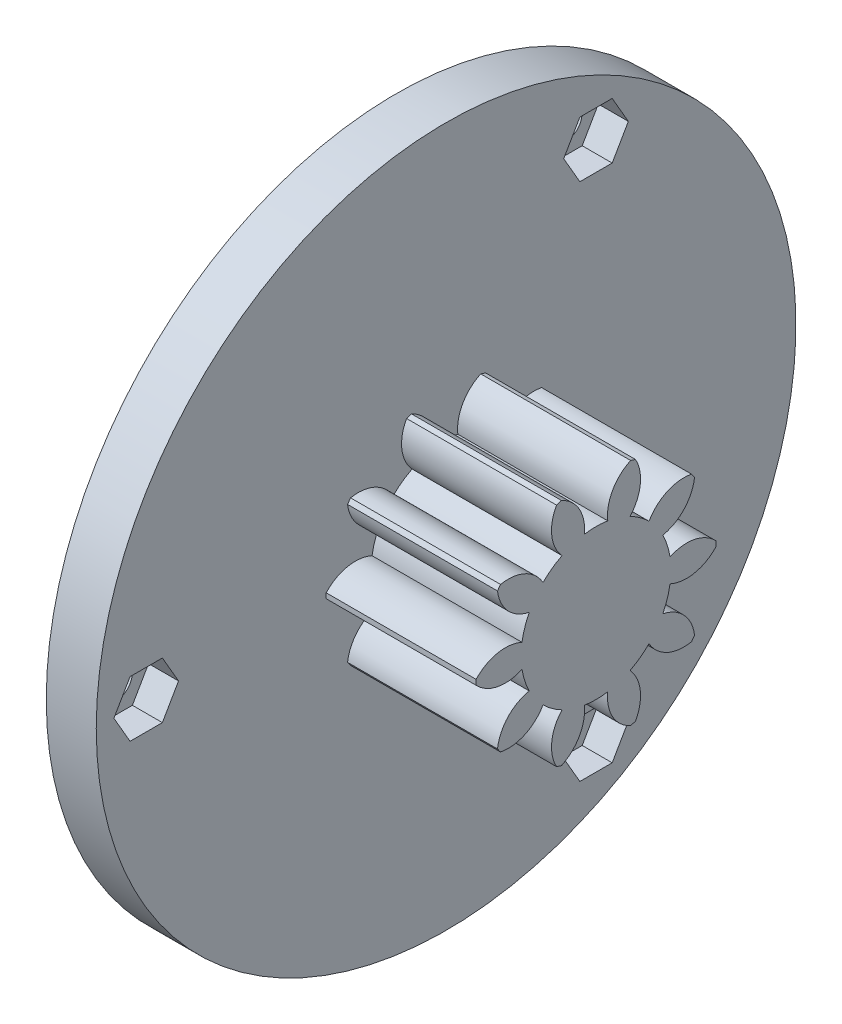
SolidWorks part; units mm, degrees
ref_plane "Plane1" through (0, 0, 0) normal (0, 0, 1) x (1, 0, 0)
ref_plane "Plane2" through (0, 0, 0) normal (0, 1, 0) x (1, 0, 0)
ref_plane "Plane3" through (0, 0, 0) normal (1, 0, 0) x (0, 0, -1)
other "Configuration Table"
sketch "HoldingSke" plane through (0, 0, 0) normal (0, 1, 0) x (1, 0, 0)
  line L0 (0, 0) -> (0.4924, -0.0868)
  line L1 (-15, 0) -> (100, 0) construction
  line L2 (0, 0) -> (-2.1039, 2.3779)
  line L3 (0, 0) -> (-11.863, 4.5341)
  line L4 (0, 0) -> (8.5048, 1.4996)
  line L5 (0, 0) -> (-46.8476, -17.4728)
  line L6 (0, 0) -> (-12.4344, -8.3896)
  line L7 (-2.1039, 2.3779) -> (8.6586, 51.2059)
  line L8 (-76.2, 54.61) -> (-76.1, 54.61)
  line L9 (-71.009, 38.7566) -> (-53.1078, 45.2721)
  line L10 (-76.2, 71.12) -> (104.1128, 71.12)
  line L11 (0, 0) -> (-15, 0)
  line L12 (-76.2, 101.6) -> (-76.133, 101.6)
  line L13 (24.9733, 27.94) -> (52.9518, 28.4284)
  line L14 (24.9733, 27.94) -> (24.9743, 27.94)
  line L15 (24.9733, 27.94) -> (100.4006, 29.5858)
  line L16 (-63.627, -2) -> (-12.827, -2)
  circle A0 centre (0, 0) radius 0.45
  circle A1 centre (0, 0) radius 7.499
  circle A2 centre (0, 0) radius 37.5
  circle A3 centre (0, 0) radius 0.45
  dimension "MHD" = 14.998
  dimension "Hub_dia" = 75
  dimension "Bore" = 0.9
  dimension "MBD" = 0.9
  dimension "Num_teeth" = 10
  dimension "Pitch" = 0.5
  dimension "Overall_len" = 50
  dimension "Show_teeth" = 10
  dimension "Thickness" = 15
  dimension "OAL" = 50.0001
  dimension "T_dim" = 0.1
  dimension "Ap" = 20
  dimension "H" = 19.05
  dimension "Pitch_radius" = 180.3128
  dimension "Width" = 15
  dimension "Backlash" = 0.067
  dimension "Addendum_fac" = 1
  dimension "Dedendum_fac" = 1.25
  dimension "Clearance_fac" = 0.25
  dimension "Dedendum_add" = 0.001
  dimension "Module" = 2
sketch "BasProSke" plane through (0, 0, 0) normal (0, 1, 0) x (1, 0, 0)
  line L0 (-10, 0) -> (60, 0) construction
  line L1 (0, 0) -> (0, 12)
  line L2 (0, 0) -> (15, 0)
  line L3 (15, 0) -> (15, 12)
  line L4 (15, 12) -> (0, 12)
  dimension "Thickness" = 15
  dimension "Diameter" = 24
revolve "Base-Revolve" add sketch "BasProSke" angle 360 about L0
sketch "TooCutSke" plane through (0, 0, 0) normal (1, 0, 0) x (0, 0, -1)
  line L1 (0, 0) -> (0, 107) construction
  line L2 (0, 0) -> (-1.6814, 9.8576) construction
  line L3 (0, 0) -> (-6.1153, 18.8209) construction
  line L4 (-1.6814, 9.8576) -> (-3.0576, 9.4105) construction
  arc A0 (1.1737, 7.4066) -> (-1.1737, 7.4066) centre (0, 0) ccw
  arc A1 (3.4979, 11.5054) -> (-3.4979, 11.5054) centre (0, 0) ccw
  circle A2 centre (0, 0) radius 10 construction
  circle A3 centre (0, 0) radius 9.3969 construction
  arc A4 (-1.1737, 7.4066) -> (-3.4979, 11.5054) centre (-5.1477, 7.8615) ccw
  arc A5 (3.4979, 11.5054) -> (1.1737, 7.4066) centre (5.1477, 7.8615) ccw
  dimension "Root_dia" = 14.998
  dimension "Overcut_dia" = 24.0508
  dimension "Pitch_dia" = 20
  dimension "Base_dia" = 18.7939
  dimension "Flank_rad" = 4
  dimension "Half_ang" = 18
  dimension "Half_CT" = 1.4471
extrude "ToothCut" cut sketch "TooCutSke" along normal through all
fillet "Breaks" [suppressed] radius 0.04
fillet "RootFillets" [suppressed] radius 0.501
pattern_circular "TeethCuts" count 10 every 36 about axis through (-10, 0, 0) along (1, 0, 0) of "ToothCut", "RootFillets", "Breaks"
sketch "HubNeaOneSke" plane through (0, 0, 0) normal (-1, 0, 0) x (0, 0, 1)
  circle A0 centre (0, 0) radius 7.499
  dimension "Diameter" = 14.998
extrude "HubNearOne" [suppressed] add sketch "HubNeaOneSke" along normal blind 35.0001
sketch "HubNeaBotSke" plane through (0, 0, 0) normal (-1, 0, 0) x (0, 0, 1)
  circle A0 centre (0, 0) radius 7.499
  dimension "Diameter" = 14.998
extrude "HubNearBoth" [suppressed] add sketch "HubNeaBotSke" along normal blind 17.5
ref_plane "FarPln" through (15, 0, 0) normal (1, 0, 0) x (0, 0, -1)
sketch "HubFarSke" plane through (15, 0, 0) normal (1, 0, 0) x (0, 0, -1)
  circle A0 centre (0, 0) radius 7.499
  dimension "Diameter" = 14.998
extrude "HubFar" [suppressed] add sketch "HubFarSke" along normal blind 17.5
sketch "BorSke" plane through (0, 0, 0) normal (1, 0, 0) x (0, 0, -1)
  circle A0 centre (0, 0) radius 0.45
  dimension "Diameter" = 0.9
extrude "Bore" cut sketch "BorSke" along normal mid plane 100.0001
sketch "KeySke" plane through (0, 0, 0) normal (1, 0, 0) x (0, 0, -1)
  line L0 (-0.05, 0) -> (-0.05, 0.55)
  line L1 (-0.05, 0.55) -> (0.05, 0.55)
  line L2 (0.05, 0.55) -> (0.05, 0)
  line L3 (0, 0) -> (0, 34) construction
  line L4 (-0.05, 0) -> (0.05, 0)
  dimension "Offset" = 0.55
  dimension "Width" = 0.1
extrude "Keyway" [suppressed] cut sketch "KeySke" along normal mid plane 100.0001
pattern_circular "Keyway2" [suppressed] count 2 every 90 about axis through (-10, 0, 0) along (1, 0, 0)
sketch "Sketch1" plane through (0, 0, 0) normal (-1, 0, 0) x (0, 0, 1)
  line L0 (0, 0) -> (0, 2.3) construction
  line L1 (-1.2124, 2.3) -> (1.2124, 2.3)
  circle A0 centre (0, 0) radius 2.6
  point P7 (0, 2.3)
extrude "Cut-Extrude1" cut sketch "Sketch1" against normal blind 15
sketch "Sketch2" plane through (0, 0, 0) normal (-1, 0, 0) x (0, 0, 1)
  circle A0 centre (0, 0) radius 3.9911
extrude "Boss-Extrude1" add sketch "Sketch2" against normal blind 15
sketch "Sketch3" plane through (0, 0, 0) normal (-1, 0, 0) x (0, 0, 1)
  circle A0 centre (0, 0) radius 35
extrude "Boss-Extrude2" add sketch "Sketch3" along normal blind 5
sketch "Sketch7" plane through (-5, 0, 0) normal (-1, 0, 0) x (0, 0, 1)
  circle A0 centre (0, 0) radius 30
  circle A2 centre (30, 0) radius 1.6
  circle A5 centre (-15, -25.9808) radius 1.6
  circle A6 centre (-15, 25.9808) radius 1.6
  point P12 (0, 0)
  point P14 (0, 0)
  dimension "D1" = 3
extrude "Cut-Extrude2" cut sketch "Sketch7" against normal blind 10 contours A6 | A2 | A5
sketch "Sketch8" plane through (0, 0, 0) normal (1, 0, 0) x (0, 0, -1)
  line L0 (15.8083, 27.3808) -> (14.1917, 27.3808)
  line L1 (-31.6166, 0) -> (-30.8083, -1.4)
  line L2 (-30.8083, -1.4) -> (-29.1917, -1.4)
  line L3 (-29.1917, -1.4) -> (-28.3834, 0)
  line L4 (-28.3834, 0) -> (-29.1917, 1.4)
  line L5 (-29.1917, 1.4) -> (-30.8083, 1.4)
  line L6 (-30.8083, 1.4) -> (-31.6166, 0)
  line L7 (14.1917, 27.3808) -> (13.3834, 25.9808)
  line L8 (13.3834, 25.9808) -> (14.1917, 24.5808)
  line L9 (14.1917, 24.5808) -> (15.8083, 24.5808)
  line L10 (15.8083, 24.5808) -> (16.6166, 25.9808)
  line L11 (16.6166, 25.9808) -> (15.8083, 27.3808)
  line L12 (15.8083, -27.3808) -> (16.6166, -25.9808)
  line L13 (16.6166, -25.9808) -> (15.8083, -24.5808)
  line L14 (15.8083, -24.5808) -> (14.1917, -24.5808)
  line L15 (14.1917, -24.5808) -> (13.3834, -25.9808)
  line L16 (13.3834, -25.9808) -> (14.1917, -27.3808)
  line L17 (14.1917, -27.3808) -> (15.8083, -27.3808)
  circle A0 centre (-30, 0) radius 1.4 construction
  point P24 (0, 0)
  dimension "D1" = 3
extrude "Cut-Extrude3" cut sketch "Sketch8" against normal blind 3
sketch "Sketch9" plane through (0, 0, 0) normal (1, 0, 0) x (0, 0, -1)
  line L0 (16.6166, 28.7808) -> (13.3834, 28.7808)
  line L1 (-33.2332, 0) -> (-31.6166, -2.8)
  line L2 (-31.6166, -2.8) -> (-28.3834, -2.8)
  line L3 (-28.3834, -2.8) -> (-26.7668, 0)
  line L4 (-26.7668, 0) -> (-28.3834, 2.8)
  line L5 (-28.3834, 2.8) -> (-31.6166, 2.8)
  line L6 (-31.6166, 2.8) -> (-33.2332, 0)
  line L7 (13.3834, 28.7808) -> (11.7668, 25.9808)
  line L8 (11.7668, 25.9808) -> (13.3834, 23.1808)
  line L9 (13.3834, 23.1808) -> (16.6166, 23.1808)
  line L10 (16.6166, 23.1808) -> (18.2332, 25.9808)
  line L11 (18.2332, 25.9808) -> (16.6166, 28.7808)
  line L12 (16.6166, -28.7808) -> (18.2332, -25.9808)
  line L13 (18.2332, -25.9808) -> (16.6166, -23.1808)
  line L14 (16.6166, -23.1808) -> (13.3834, -23.1808)
  line L15 (13.3834, -23.1808) -> (11.7668, -25.9808)
  line L16 (11.7668, -25.9808) -> (13.3834, -28.7808)
  line L17 (13.3834, -28.7808) -> (16.6166, -28.7808)
  circle A0 centre (-30, 0) radius 2.8 construction
  point P24 (0, 0)
  dimension "D1" = 3
extrude "Cut-Extrude5" cut sketch "Sketch9" against normal blind 3
equation "' \"Module@HoldingSke\" = 6.35"
equation "' \"Num_teeth@HoldingSke\" = 12"
equation "' \"Ap@HoldingSke\" =  20"
equation "' \"Ap@HoldingSke\" = 20"
equation "' \"Width@HoldingSke\" = 0.5 * 25.4"
equation "' \"Hub_dia@HoldingSke\"= 1 * 25.4"
equation "' \"Hub_dia@HoldingSke\" = 1 * 25.4"
equation "' \"Overall_len@HoldingSke\" = 1.0 * 25.4"
equation "' \"Bore@HoldingSke\" = 0.75 * 25.4"
equation "' \"T_dim@HoldingSke\" = 0.1 * 25.4"
equation "' \"Width@KeySke\" = 0.25 * 25.4"
equation "' \"Show_teeth@HoldingSke\" = 13"
equation "' \"Backlash@HoldingSke\" = 0.009 * 25.4"
equation "' \"Addendum_fac@HoldingSke\" = 1.0"
equation "' \"Dedendum_fac@HoldingSke\" = 1.25"
equation "' \"Dedendum_add@HoldingSke\" = 0.00005 * 25.4"
equation "' \"Clearance_fac@HoldingSke\" = 0.25"
equation "\"Pitch@HoldingSke\" = 1 / \"Module@HoldingSke\""
equation "\"Overcut_dia@TooCutSke\" = (\"Num_teeth@HoldingSke\" + 2 * \"Addendum_fac@HoldingSke\") / \"Pitch@HoldingSke\" + 0.002 * 25.4"
equation "\"Pitch_dia@TooCutSke\" = \"Num_teeth@HoldingSke\" / \"Pitch@HoldingSke\""
equation "\"Base_dia@TooCutSke\" = \"Num_teeth@HoldingSke\" / \"Pitch@HoldingSke\" * cos((\"Ap@HoldingSke\"  * 3.14159265 / 180))"
equation "\"Root_dia@TooCutSke\" = (\"Num_teeth@HoldingSke\" + 2) / \"Pitch@HoldingSke\" - 2 * (\"Addendum_fac@HoldingSke\" + \"Dedendum_fac@HoldingSke\") / \"Pitch@HoldingSke\" - \"Dedendum_add@HoldingSke\" * 2"
equation "\"Half_ang@TooCutSke\" = 180 / \"Num_teeth@HoldingSke\""
equation "\"Half_CT@TooCutSke\" = \"Num_teeth@HoldingSke\" / \"Pitch@HoldingSke\" * sin((3.14159265 / 2 / \"Num_teeth@HoldingSke\")) / 2 - 7 * \"Backlash@HoldingSke\" / 4"
equation "\"Flank_rad@TooCutSke\" = \"Num_teeth@HoldingSke\" / \"Pitch@HoldingSke\" / 5"
equation "\"Radius@RootFillets\" = \"Clearance_fac@HoldingSke\" / \"Pitch@HoldingSke\" + \"Dedendum_add@HoldingSke\""
equation "\"Break_rad@Breaks\" = 0.02 / \"Pitch@HoldingSke\""
equation "\"Thickness@HoldingSke\" = \"Width@HoldingSke\""
equation "\"OAL@HoldingSke\" = \"Thickness@HoldingSke\""
equation "\"MHD@HoldingSke\" = (\"Num_teeth@HoldingSke\" + 2) / \"Pitch@HoldingSke\" - 2 * (\"Addendum_fac@HoldingSke\" + \"Dedendum_fac@HoldingSke\")  / \"Pitch@HoldingSke\" - \"Dedendum_add@HoldingSke\" * 2"
equation "\"MBD@HoldingSke\" = (\"Num_teeth@HoldingSke\" + 2) / \"Pitch@HoldingSke\" - 2 * (\"Addendum_fac@HoldingSke\" + \"Dedendum_fac@HoldingSke\")  / \"Pitch@HoldingSke\" - \"Dedendum_add@HoldingSke\" * 2 - 0.002 * 25.4"
equation "\"MHD@HoldingSke\" = ((sgn( \"MHD@HoldingSke\" - \"Hub_dia@HoldingSke\" )-1)*( \"MHD@HoldingSke\" - \"Hub_dia@HoldingSke\" ))/-2+ \"Hub_dia@HoldingSke\""
equation "\"MBD@HoldingSke\" = ((sgn( \"MBD@HoldingSke\" - \"Bore@HoldingSke\" )-1)*( \"MBD@HoldingSke\" - \"Bore@HoldingSke\" ))/-2+ \"Bore@HoldingSke\""
equation "\"OAL@HoldingSke\" = ((sgn( \"OAL@HoldingSke\" - \"Overall_len@HoldingSke\" )+1)*( \"OAL@HoldingSke\" - \"Overall_len@HoldingSke\" ))/2 + \"Overall_len@HoldingSke\" + 0.000002 * 25.4"
equation "\"Num_teeth@TeethCuts\" = int( \"Show_teeth@HoldingSke\" ) + 1"
equation "\"Num_teeth@TeethCuts\" = ((sgn( \"Num_teeth@TeethCuts\" - \"Num_teeth@HoldingSke\" )-1)*( \"Num_teeth@TeethCuts\" - \"Num_teeth@HoldingSke\" ))/-2+ \"Num_teeth@HoldingSke\""
equation "\"Num_teeth@TeethCuts\" = ((sgn( \"Num_teeth@TeethCuts\" - 2.0)+1)*( \"Num_teeth@TeethCuts\" - 2.0))/2 +2.0"
equation "\"Angle@TeethCuts\" = 360.0 / \"Num_teeth@HoldingSke\""
equation "\"Diameter@BasProSke\" = (\"Num_teeth@HoldingSke\" + 2 * \"Addendum_fac@HoldingSke\") / \"Pitch@HoldingSke\""
equation "\"Thickness@BasProSke\"  = \"Thickness@HoldingSke\""
equation "' \"Fillet_rad@BasProSke\" =  \"Thickness@HoldingSke\" * 0.05"
equation "' \"Fillet_rad@BasProSke\" = \"Thickness@HoldingSke\" * 0.05"
equation "\"MHD@HoldingSke\" = ((sgn( \"MHD@HoldingSke\" - \"Root_dia@TooCutSke\" )-1)*( \"MHD@HoldingSke\" - \"Root_dia@TooCutSke\" ))/-2+ \"Root_dia@TooCutSke\""
equation "\"Diameter@HubNeaOneSke\" = \"MHD@HoldingSke\""
equation "\"Length@HubNearOne\" = \"OAL@HoldingSke\" - \"Thickness@BasProSke\""
equation "\"Diameter@HubNeaBotSke\" = \"MHD@HoldingSke\""
equation "\"Length@HubNearBoth\" = ( \"OAL@HoldingSke\" - \"Thickness@BasProSke\" ) / 2.0"
equation "\"Thickness@FarPln\" = \"Thickness@BasProSke\""
equation "\"Diameter@HubFarSke\" = \"MHD@HoldingSke\""
equation "\"Length@HubFar\" = ( \"OAL@HoldingSke\" - \"Thickness@BasProSke\" ) / 2.0"
equation "\"Diameter@BorSke\" = \"MBD@HoldingSke\""
equation "\"D1@Bore\" = \"OAL@HoldingSke\" * 2.0"
equation "\"D1@Keyway\" = \"OAL@HoldingSke\" * 2.0"
equation "\"Offset@KeySke\" = \"T_dim@HoldingSke\" + \"MBD@HoldingSke\" / 2.0"
